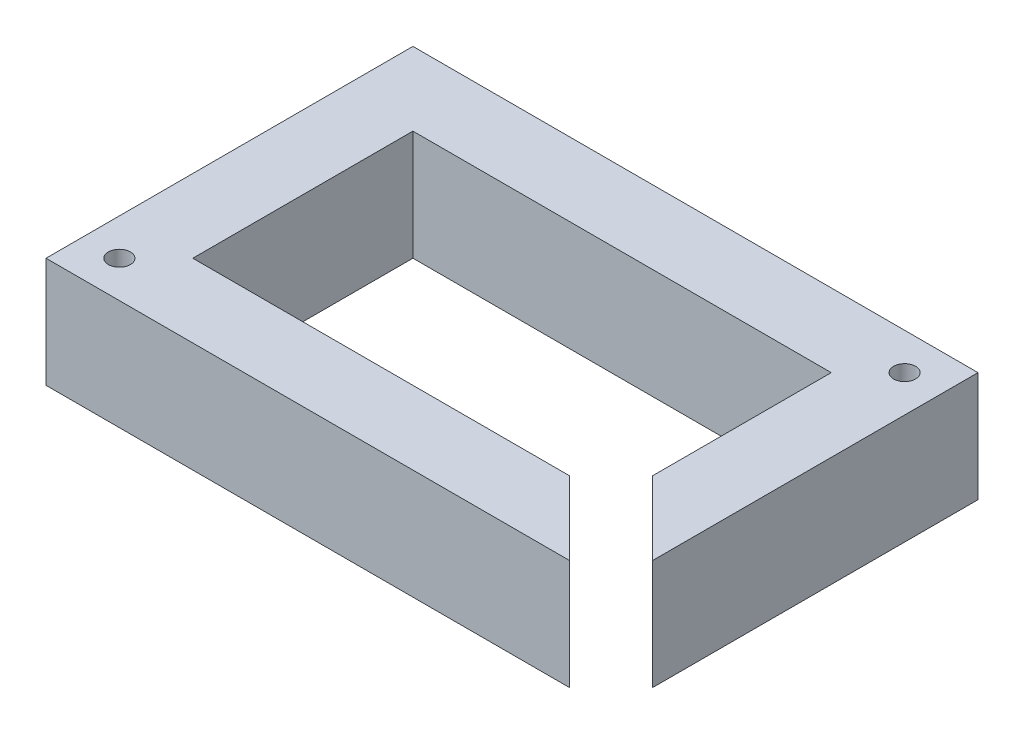
SolidWorks part; units mm, degrees
ref_plane "Front Plane" through (0, 0, 0) normal (0, 0, 1) x (1, 0, 0)
ref_plane "Top Plane" through (0, 0, 0) normal (0, 1, 0) x (1, 0, 0)
ref_plane "Right Plane" through (0, 0, 0) normal (1, 0, 0) x (0, 0, -1)
sketch "Sketch1" plane through (0, 0, 0) normal (0, 1, 0) x (1, 0, 0)
  line L0 (-10, 40) -> (67, 40)
  line L1 (0, 0) -> (57, 0)
  line L2 (0, 0) -> (0, 30)
  line L3 (0, 30) -> (57, 30)
  line L4 (57, 0) -> (57, 30)
  line L5 (67, -10) -> (67, 40)
  line L6 (-10, -10) -> (67, -10)
  line L7 (-10, -10) -> (-10, 40)
  line L8 (57, 0) -> (67, -10)
  line L9 (51.3431, 0) -> (64.1716, -12.8284)
  line L10 (57, 5.6569) -> (69.8284, -7.1716)
  line L11 (59.8284, 2.8284) -> (69.8284, -7.1716) construction
  line L12 (54.1716, -2.8284) -> (64.1716, -12.8284) construction
  circle A0 centre (-5, -5) radius 1.5
  circle A1 centre (62, 35) radius 1.5
  dimension "D4" = 3
  dimension "D5" = 3
  dimension "D1" = 57
  dimension "D2" = 30
  dimension "D6" = 5
  dimension "D7" = 5
  dimension "D8" = 5
  dimension "D9" = 5
  dimension "D3" = 10
  dimension "D10" = 4
  dimension "D11" = 4
extrude "Boss-Extrude1" add sketch "Sketch1" along normal blind 15 contours L4 L10 L5 L0 L7 L6 L9 L1 L2 L3 A1 A0
